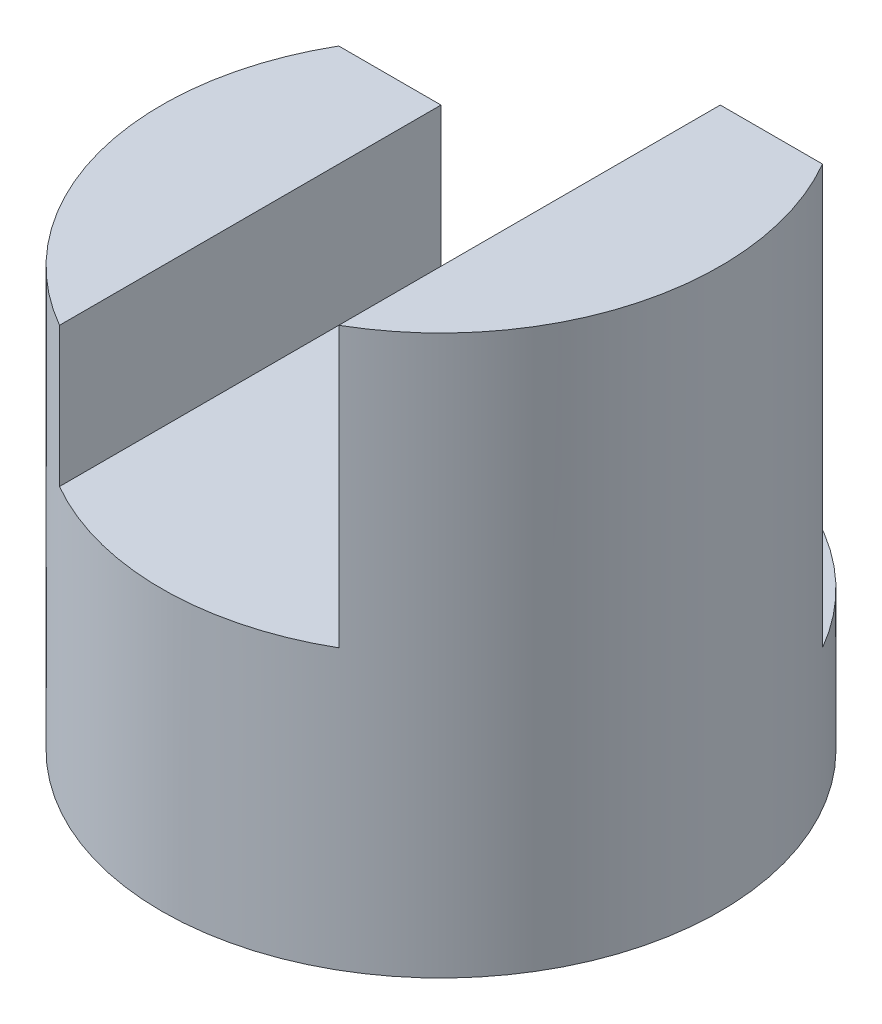
SolidWorks part; units mm, degrees
ref_plane "Front" through (0, 0, 0) normal (0, 0, 1) x (1, 0, 0)
ref_plane "Top" through (0, 0, 0) normal (0, 1, 0) x (1, 0, 0)
ref_plane "Right" through (0, 0, 0) normal (1, 0, 0) x (0, 0, -1)
sketch "Sketch1" plane through (0, 0, 0) normal (0, 1, 0) x (1, 0, 0)
  circle A0 centre (0, 0) radius 2
  dimension "D1" = 4
extrude "Boss-Extrude1" add sketch "Sketch1" along normal blind 4
sketch "Sketch3" plane through (0, 4, 0) normal (0, 1, 0) x (1, 0, 0)
  line L0 (-1.7321, 1) -> (1.7321, 1)
  arc A0 (-1.7321, 1) -> (1.7321, 1) centre (0, 0) cw
  point P5 (0, 0)
  point P6 (0, 0)
  point P8 (0, 0)
extrude "Cut-Extrude2" cut sketch "Sketch3" against normal blind 3
sketch "Sketch4" plane through (0, 0, 0) normal (0, 0, 1) x (1, 0, 0)
  line L0 (-2, 3) -> (-1, 3)
  line L1 (-2, 4) -> (-2, 0) construction
  line L2 (-1, 3) -> (-1, 2)
  line L3 (-1, 2) -> (1, 2)
  line L4 (1, 2) -> (1, 4)
  line L5 (2, 4) -> (-2, 4) construction
  line L6 (1, 4) -> (-2, 4)
  line L7 (-2, 4) -> (-2, 3)
  line L8 (2, 0) -> (2, 4) construction
  dimension "D1" = 1
  dimension "D2" = 1
  dimension "D3" = 2
  dimension "D4" = 1
extrude "Cut-Extrude3" cut sketch "Sketch4" against normal mid plane 11
